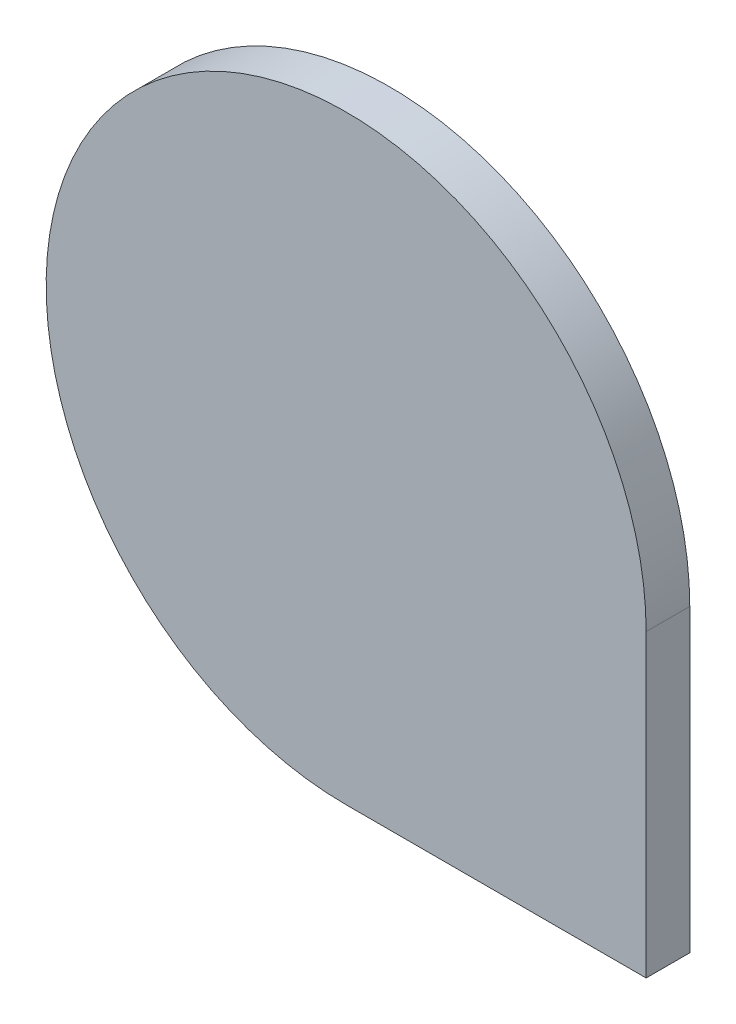
SolidWorks part; units mm, degrees
ref_plane "Front Plane" through (0, 0, 0) normal (0, 0, 1) x (1, 0, 0)
ref_plane "Top Plane" through (0, 0, 0) normal (0, 1, 0) x (1, 0, 0)
ref_plane "Right Plane" through (0, 0, 0) normal (1, 0, 0) x (0, 0, -1)
sketch "Sketch1" plane through (0, 0, 0) normal (0, 0, 1) x (1, 0, 0)
  line L0 (55, 0) -> (55, -55)
  line L1 (55, -55) -> (0, -55)
  arc A0 (55, 0) -> (0, -55) centre (0, 0) ccw
  point P4 (0, 0)
  point P5 (0, 0)
  dimension "D1" = 110
extrude "Boss-Extrude1" add sketch "Sketch1" along normal blind 8
